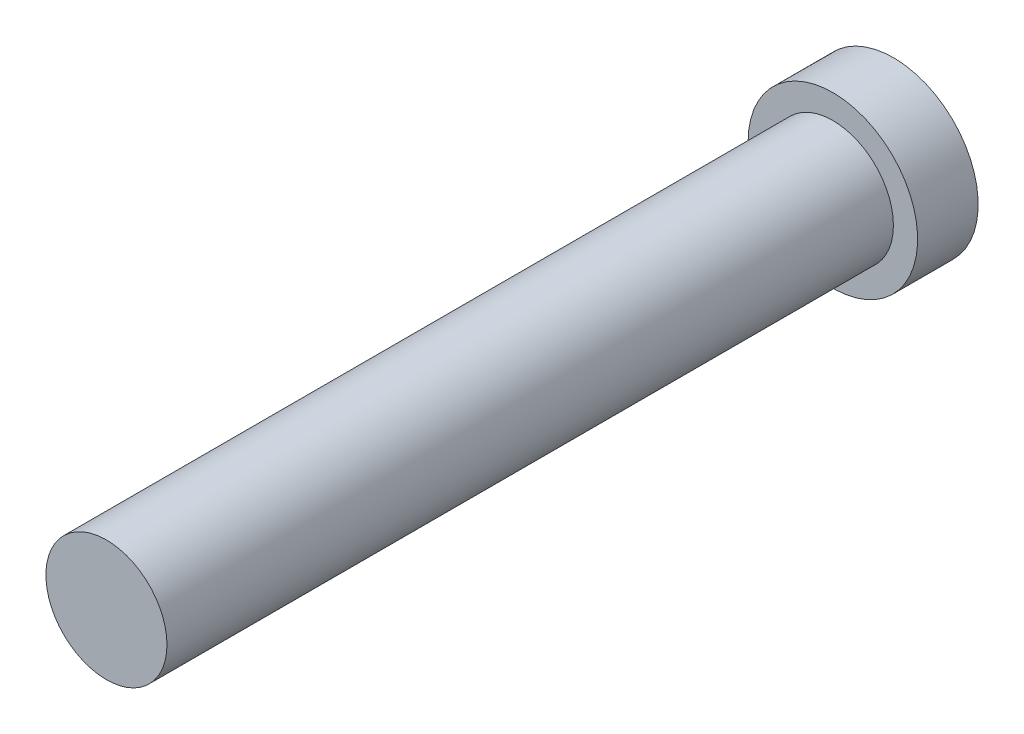
SolidWorks part; units mm, degrees
ref_plane "Front Plane" through (0, 0, 0) normal (0, 0, 1) x (1, 0, 0)
ref_plane "Top Plane" through (0, 0, 0) normal (0, 1, 0) x (1, 0, 0)
ref_plane "Right Plane" through (0, 0, 0) normal (1, 0, 0) x (0, 0, -1)
sketch "Sketch1" plane through (0, 0, 0) normal (0, 0, 1) x (1, 0, 0)
  circle A0 centre (0, 0) radius 2.5
  dimension "D1" = 5
extrude "Boss-Extrude1" add sketch "Sketch1" along normal blind 30
sketch "Sketch2" plane through (0, 0, 0) normal (0, 0, -1) x (-1, 0, 0)
  circle A0 centre (0, 0) radius 3.5
  dimension "D1" = 7
extrude "Boss-Extrude2" add sketch "Sketch2" along normal blind 2.5
